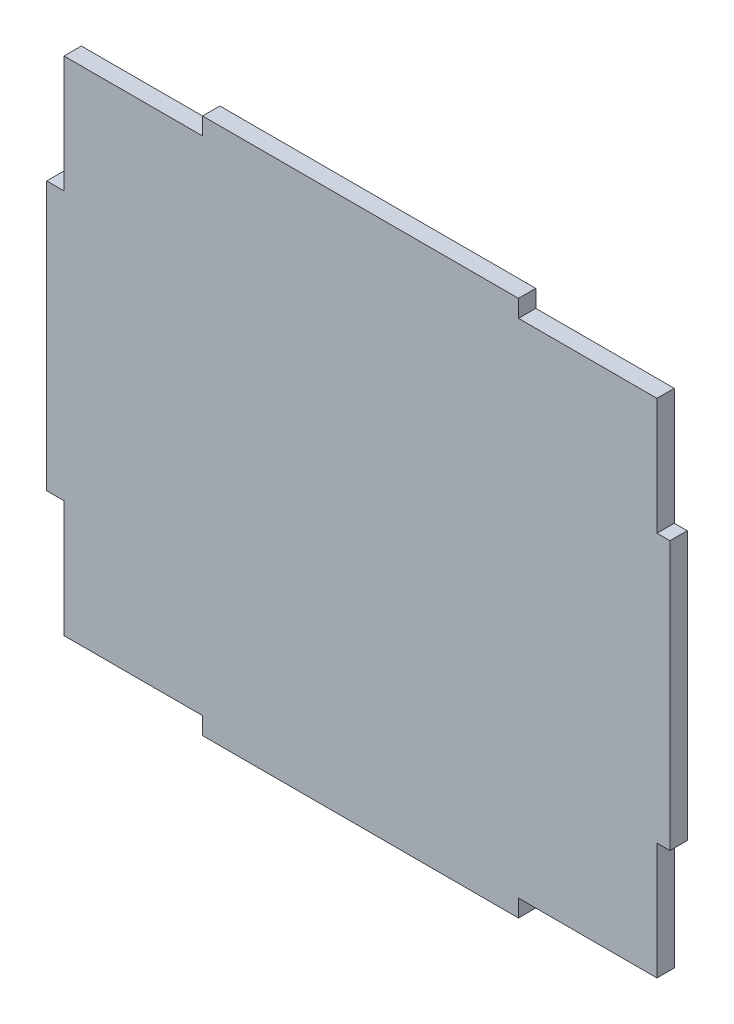
SolidWorks part; units mm, degrees
ref_plane "正面" through (0, 0, 0) normal (0, 0, 1) x (1, 0, 0)
ref_plane "平面" through (0, 0, 0) normal (0, 1, 0) x (1, 0, 0)
ref_plane "右側面" through (0, 0, 0) normal (1, 0, 0) x (0, 0, -1)
sketch "ｽｹｯﾁ1" plane through (0, 0, 0) normal (0, 0, 1) x (1, 0, 0)
  line L1 (-37.0426, 40.7363) -> (34.9574, 40.7363)
  line L2 (-37.0426, 40.7363) -> (-37.0426, -21.2637)
  line L3 (-37.0426, -21.2637) -> (34.9574, -21.2637)
  line L4 (34.9574, 40.7363) -> (34.9574, -21.2637)
  dimension "D1" = 72
  dimension "D2" = 62
extrude "ﾎﾞｽ - 押し出し1" add sketch "ｽｹｯﾁ1" along normal blind 2
sketch "ｽｹｯﾁ2" plane through (0, 0, 2) normal (0, 0, 1) x (1, 0, 0)
  line L0 (33.4574, 40.7363) -> (33.4574, 25.2363) construction
  line L1 (35.4574, -21.2637) -> (33.4574, -21.2637)
  line L2 (35.4574, -21.2637) -> (35.4574, -5.7637)
  line L3 (35.4574, -5.7637) -> (33.4574, -5.7637)
  line L4 (33.4574, -21.2637) -> (33.4574, -5.7637)
  line L5 (-35.0426, 40.7363) -> (-35.0426, 25.2363) construction
  line L6 (35.4574, 40.7363) -> (33.4574, 40.7363)
  line L7 (35.4574, 40.7363) -> (35.4574, 25.2363)
  line L8 (35.4574, 25.2363) -> (33.4574, 25.2363)
  line L9 (33.4574, 40.7363) -> (33.4574, 25.2363)
  line L10 (-37.0426, 40.7363) -> (-35.0426, 40.7363)
  line L11 (-37.0426, 40.7363) -> (-37.0426, 25.2363)
  line L12 (-37.0426, 25.2363) -> (-35.0426, 25.2363)
  line L13 (-35.0426, 40.7363) -> (-35.0426, 25.2363)
  line L15 (-37.0426, -21.2637) -> (-35.0426, -21.2637)
  line L16 (-37.0426, -21.2637) -> (-37.0426, -5.7637)
  line L17 (-37.0426, -5.7637) -> (-35.0426, -5.7637)
  line L18 (-35.0426, -21.2637) -> (-35.0426, -5.7637)
  dimension "D1" = 15.5
  dimension "D2" = 15.5
  dimension "D3" = 15.5
  dimension "D4" = 15.5
extrude "ｶｯﾄ - 押し出し1" cut sketch "ｽｹｯﾁ2" against normal through all
sketch "ｽｹｯﾁ3" plane through (0, 0, 2) normal (0, 0, 1) x (1, 0, 0)
  line L0 (33.4574, 38.7363) -> (17.4574, 38.7363) construction
  line L1 (-37.0426, 40.7363) -> (-19.0426, 40.7363)
  line L2 (-37.0426, 40.7363) -> (-37.0426, 38.7363)
  line L3 (-37.0426, 38.7363) -> (-19.0426, 38.7363)
  line L4 (-19.0426, 40.7363) -> (-19.0426, 38.7363)
  line L5 (-35.0426, -19.2637) -> (-19.0426, -19.2637) construction
  line L6 (35.4574, 40.7363) -> (17.4574, 40.7363)
  line L7 (35.4574, 40.7363) -> (35.4574, 38.7363)
  line L8 (35.4574, 38.7363) -> (17.4574, 38.7363)
  line L9 (17.4574, 40.7363) -> (17.4574, 38.7363)
  line L10 (-37.0426, -21.2637) -> (-19.0426, -21.2637)
  line L11 (-37.0426, -21.2637) -> (-37.0426, -19.2637)
  line L12 (-37.0426, -19.2637) -> (-19.0426, -19.2637)
  line L13 (-19.0426, -21.2637) -> (-19.0426, -19.2637)
  line L15 (35.4574, -21.2637) -> (17.4574, -21.2637)
  line L16 (35.4574, -21.2637) -> (35.4574, -19.2637)
  line L17 (35.4574, -19.2637) -> (17.4574, -19.2637)
  line L18 (17.4574, -21.2637) -> (17.4574, -19.2637)
  dimension "D1" = 18
  dimension "D2" = 18
  dimension "D3" = 18
  dimension "D4" = 18
extrude "ｶｯﾄ - 押し出し2" cut sketch "ｽｹｯﾁ3" against normal through all
